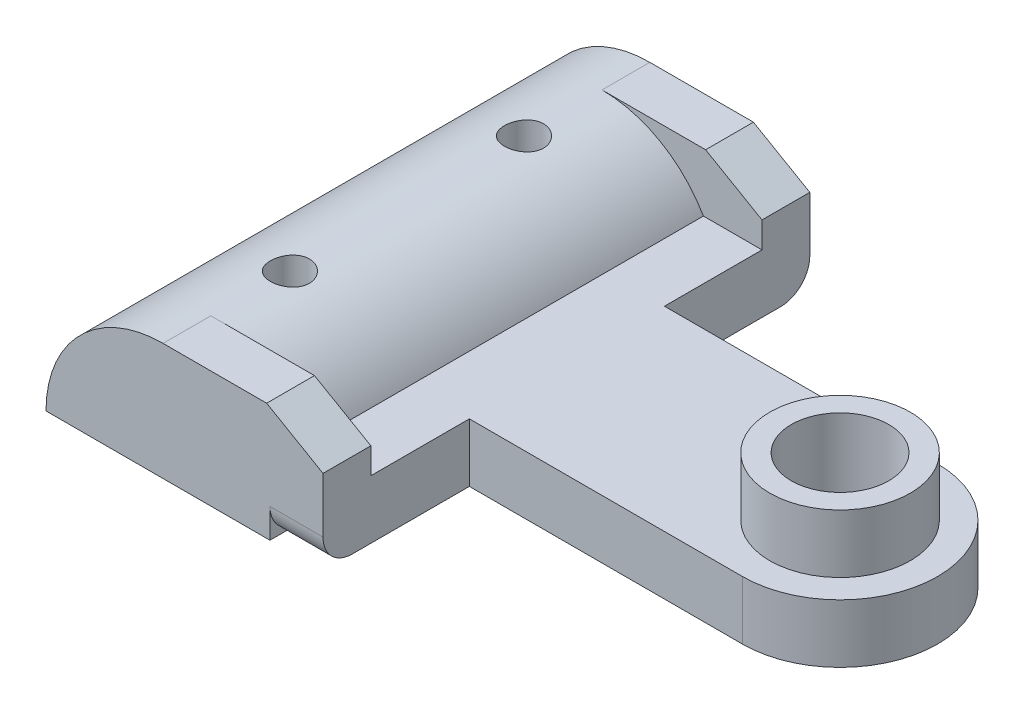
SolidWorks part; units mm, degrees
ref_plane "Alzado" through (0, 0, 0) normal (0, 0, 1) x (1, 0, 0)
ref_plane "Planta" through (0, 0, 0) normal (0, 1, 0) x (1, 0, 0)
ref_plane "Vista lateral" through (0, 0, 0) normal (1, 0, 0) x (0, 0, -1)
sketch "Croquis1" plane through (0, 0, 0) normal (0, 1, 0) x (1, 0, 0)
  line L0 (-16.8477, 12.8466) -> (-2.6477, 12.8466)
  line L1 (-16.8477, 12.8466) -> (-16.8477, -12.1034)
  line L2 (-16.8477, -12.1034) -> (-2.6477, -12.1034)
  line L3 (-2.6477, 12.8466) -> (-2.6477, 5.3966)
  line L4 (11.3523, -4.6034) -> (-2.6477, -4.6034)
  line L5 (11.3523, 5.3966) -> (-2.6477, 5.3966)
  line L6 (-2.6477, -4.6034) -> (-2.6477, -12.1034)
  arc A0 (11.3523, -4.6034) -> (11.3523, 5.3966) centre (11.3523, 0.3966) ccw
  circle A1 centre (11.3523, 0.3966) radius 2.5
  circle A2 centre (-10.8477, 6.3966) radius 1
  circle A3 centre (-10.8477, -5.6034) radius 1
extrude "Saliente-Extruir1" add sketch "Croquis1" along normal blind 3
sketch "Croquis2" plane through (0, 0, 12.1034) normal (0, 0, 1) x (1, 0, 0)
  line L0 (-16.8477, 0) -> (-2.6477, 0) construction
  line L1 (-16.0439, 3) -> (-5.6516, 3)
  line L2 (-16.8477, 3) -> (-2.6477, 3) construction
  arc A0 (-5.6516, 3) -> (-16.0439, 3) centre (-10.8477, 0) ccw
  dimension "D1" = 12
extrude "Saliente-Extruir2" add sketch "Croquis2" against normal up to surface (24.95 mm away) up to face at (-9.7477, 1.5, -12.8466)
sketch "Croquis3" plane through (0, 3, 0) normal (0, 1, 0) x (1, 0, 0)
  line L0 (-16.8477, 12.8466) -> (-16.8477, -12.1034) construction
  line L1 (-2.6477, 12.8466) -> (-10.8477, 12.8466)
  line L2 (-2.6477, 12.8466) -> (-2.6477, 10.3966)
  line L3 (-2.6477, 10.3966) -> (-10.8477, 10.3966)
  line L4 (-10.8477, 12.8466) -> (-10.8477, 10.3966)
  line L5 (-2.6477, -12.1034) -> (-10.8477, -12.1034)
  line L6 (-2.6477, -12.1034) -> (-2.6477, -9.6534)
  line L7 (-2.6477, -9.6534) -> (-10.8477, -9.6534)
  line L8 (-10.8477, -12.1034) -> (-10.8477, -9.6534)
  dimension "D1" = 2.45
  dimension "D2" = 6
extrude "Saliente-Extruir3" add sketch "Croquis3" along normal blind 3
sketch "Croquis4" plane through (0, 0, 12.1034) normal (0, 0, 1) x (1, 0, 0)
  line L0 (-2.6477, 4.33) -> (-2.6477, 6)
  line L1 (-2.6477, 6) -> (-2.6477, 0) construction
  line L2 (-2.6477, 6) -> (-5.5377, 6)
  line L3 (-10.8477, 6) -> (-2.6477, 6) construction
  line L4 (-5.5377, 6) -> (-2.6477, 4.33)
  dimension "D1" = 2.89
  dimension "D2" = 1.67
extrude "Cortar-Extruir1" cut sketch "Croquis4" against normal blind 31
sketch "Croquis5" plane through (-2.6477, 0, 0) normal (1, 0, 0) x (0, 0, -1)
  line L0 (-12.1034, 4.33) -> (-12.1034, 0) construction
  line L1 (-12.1034, 0) -> (-4.6034, 0) construction
  line L2 (5.3966, 0) -> (12.8466, 0) construction
  line L3 (12.8466, 4.33) -> (12.8466, 0) construction
  line L4 (12.8466, 1.5) -> (14.9643, 1.5)
  line L5 (-12.1034, 1.5) -> (-14.9643, 1.5)
  line L6 (-10.6034, 0) -> (11.3466, 0)
  arc A0 (-12.1034, 1.5) -> (-10.6034, 0) centre (-10.6034, 1.5) ccw
  arc A1 (11.3466, 0) -> (12.8466, 1.5) centre (11.3466, 1.5) ccw
  arc A2 (-14.9643, 1.5) -> (14.9643, 1.5) centre (0, 0.1727) ccw
  dimension "D1" = 3
extrude "Cortar-Extruir2" cut sketch "Croquis5" against normal blind 2.72
sketch "Croquis6" plane through (0, 3, 0) normal (0, 1, 0) x (1, 0, 0)
  circle A0 centre (11.3523, 0.3966) radius 3.6
  circle A1 centre (11.3523, 0.3966) radius 2.5 construction
  circle A2 centre (11.3523, 0.3966) radius 2.5
  dimension "D1" = 7.2
extrude "Saliente-Extruir4" add sketch "Croquis6" along normal blind 3
sketch "Croquis7" plane through (0, 0, 12.1034) normal (0, 0, 1) x (1, 0, 0)
  line L0 (-16.8477, 0) -> (-5.3677, 0) construction
  line L1 (-12.7589, 7.2887) -> (-12.3695, 5.8038)
  line L2 (-16.8477, 0) -> (-18.3829, 0)
  arc A0 (-12.3695, 5.8038) -> (-16.8477, 0) centre (-10.8477, 0) ccw
  arc A1 (-12.7589, 7.2887) -> (-18.3829, 0) centre (-10.8477, 0) ccw
  dimension "D1" = 12
extrude "Cortar-Extruir3" cut sketch "Croquis7" against normal blind 27
sketch "Croquis8" plane through (0, 0, 0) normal (0, -1, 0) x (1, 0, 0)
  circle A0 centre (-10.8477, -6.3966) radius 1 construction
  circle A1 centre (-10.8477, 5.6034) radius 1 construction
  circle A2 centre (-10.8477, -6.3966) radius 1
  circle A3 centre (-10.8477, 5.6034) radius 1
extrude "Cortar-Extruir4" cut sketch "Croquis8" against normal blind 27
